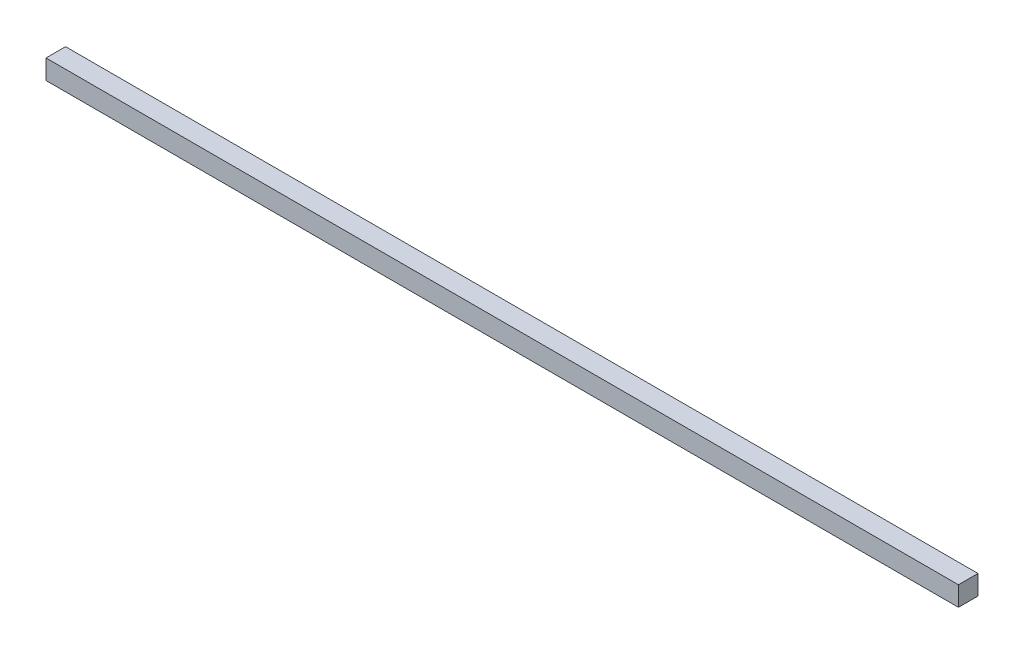
SolidWorks part; units mm, degrees
ref_plane "Front Plane" through (0, 0, 0) normal (0, 0, 1) x (1, 0, 0)
ref_plane "Top Plane" through (0, 0, 0) normal (0, 1, 0) x (1, 0, 0)
ref_plane "Right Plane" through (0, 0, 0) normal (1, 0, 0) x (0, 0, -1)
sketch "Sketch1" plane through (0, 0, 0) normal (1, 0, 0) x (0, 0, -1)
  line L1 (0, 0) -> (15, 0)
  line L2 (0, 0) -> (0, 15)
  line L3 (0, 15) -> (15, 15)
  line L4 (15, 0) -> (15, 15)
  dimension "D1" = 15
  dimension "D2" = 15
extrude "Boss-Extrude1" add sketch "Sketch1" along normal blind 700 contours L3 L4 L1 L2
